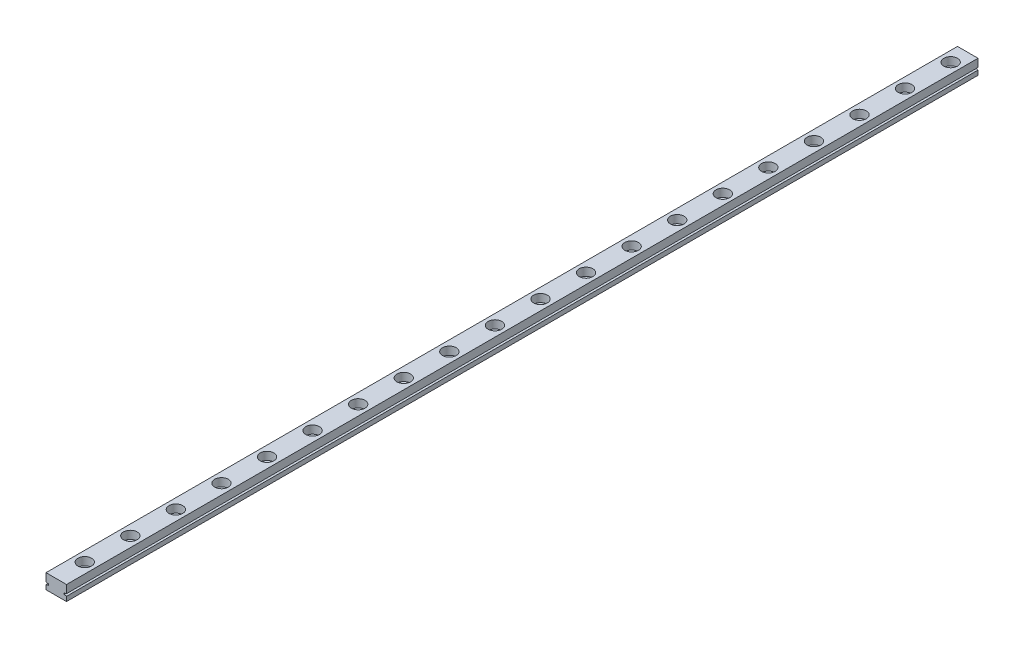
SolidWorks part; units mm, degrees
material "合金钢"
ref_plane "前视基准面" through (0, 0, 0) normal (0, 0, 1) x (1, 0, 0)
ref_plane "上视基准面" through (0, 0, 0) normal (0, 1, 0) x (1, 0, 0)
ref_plane "右视基准面" through (0, 0, 0) normal (1, 0, 0) x (0, 0, -1)
sketch "草图1" plane through (0, 0, 0) normal (0, 0, 1) x (1, 0, 0)
  line L1 (-4.5, 3.25) -> (4.5, 3.25)
  line L2 (-4.5, 3.25) -> (-4.5, -3.25)
  line L3 (-4.5, -3.25) -> (4.5, -3.25)
  line L4 (4.5, 3.25) -> (4.5, -3.25)
  line L5 (-4.5, 3.25) -> (4.5, -3.25) construction
  line L6 (-4.5, -3.25) -> (4.5, 3.25) construction
  point P0 (0, 0)
  dimension "D1" = 6.5
  dimension "D2" = 9
extrude "凸台-拉伸1" add sketch "草图1" along normal blind 400
sketch "草图2" plane through (0, 3.25, 0) normal (0, 1, 0) x (1, 0, 0)
  line L0 (0, 0) -> (0, -84.8716) construction
  line L1 (4.5, 0) -> (-4.5, 0) construction
  circle A0 centre (0, -7.5) radius 1.75
  circle A1 centre (0, -27.5) radius 1.75
  circle A2 centre (0, -47.5) radius 1.75
  circle A3 centre (0, -67.5) radius 1.75
  circle A4 centre (0, -87.5) radius 1.75
  circle A5 centre (0, -107.5) radius 1.75
  circle A6 centre (0, -127.5) radius 1.75
  circle A7 centre (0, -147.5) radius 1.75
  circle A8 centre (0, -167.5) radius 1.75
  circle A9 centre (0, -187.5) radius 1.75
  circle A10 centre (0, -207.5) radius 1.75
  circle A11 centre (0, -227.5) radius 1.75
  circle A12 centre (0, -247.5) radius 1.75
  circle A13 centre (0, -267.5) radius 1.75
  circle A14 centre (0, -287.5) radius 1.75
  circle A15 centre (0, -307.5) radius 1.75
  circle A16 centre (0, -327.5) radius 1.75
  circle A17 centre (0, -347.5) radius 1.75
  circle A18 centre (0, -367.5) radius 1.75
  dimension "D1" = 3.5
  dimension "D2" = 7.5
  dimension "D4" = 20
  dimension "D3" = 19
extrude "切除-拉伸1" cut sketch "草图2" against normal through all
sketch "草图3" plane through (0, 3.25, 0) normal (0, 1, 0) x (1, 0, 0)
  circle A0 centre (0, -7.5) radius 3
  circle A1 centre (0, -27.5) radius 3
  circle A2 centre (0, -47.5) radius 3
  circle A3 centre (0, -67.5) radius 3
  circle A4 centre (0, -87.5) radius 3
  circle A5 centre (0, -107.5) radius 3
  circle A6 centre (0, -127.5) radius 3
  circle A7 centre (0, -147.5) radius 3
  circle A8 centre (0, -167.5) radius 3
  circle A9 centre (0, -187.5) radius 3
  circle A10 centre (0, -207.5) radius 3
  circle A11 centre (0, -227.5) radius 3
  circle A12 centre (0, -247.5) radius 3
  circle A13 centre (0, -267.5) radius 3
  circle A14 centre (0, -287.5) radius 3
  circle A15 centre (0, -307.5) radius 3
  circle A16 centre (0, -327.5) radius 3
  circle A17 centre (0, -347.5) radius 3
  circle A18 centre (0, -367.5) radius 3
  circle A19 centre (0, -387.5) radius 3
  dimension "D1" = 6
  dimension "D3" = 20
  dimension "D2" = 20
extrude "切除-拉伸2" cut sketch "草图3" against normal blind 3.5
sketch "草图4" plane through (0, 0, 0) normal (0, 0, -1) x (-1, 0, 0)
  line L0 (0, 3.25) -> (0, -3.25) construction
  line L1 (-4.5, 3.25) -> (4.5, 3.25) construction
  line L2 (4.5, -3.25) -> (-4.5, -3.25) construction
  line L3 (4.5, -0.25) -> (3.5, -0.45)
  line L4 (4.5, 3.25) -> (4.5, -3.25) construction
  line L5 (3.5, -0.45) -> (3.5, -1.05)
  line L6 (3.5, -1.05) -> (4.5, -1.25)
  line L7 (3.5, -0.75) -> (7.9936, -0.75) construction
  line L8 (4.5, -0.25) -> (4.5, -1.25)
  line L9 (-4.5, -0.25) -> (-3.5, -0.45)
  line L10 (-3.5, -0.45) -> (-3.5, -1.05)
  line L11 (-3.5, -1.05) -> (-4.5, -1.25)
  line L12 (-4.5, -0.25) -> (-4.5, -1.25)
  dimension "D1" = 1
  dimension "D2" = 1
  dimension "D3" = 0.6
  dimension "D4" = 4
extrude "切除-拉伸3" cut sketch "草图4" against normal through all
sketch "草图5" plane through (0, -0.25, 0) normal (0, 1, 0) x (1, 0, 0)
  circle A0 centre (0, -387.5) radius 1.75
  circle A1 centre (0, -387.5) radius 3 construction
  dimension "D1" = 3.5
extrude "切除-拉伸4" cut sketch "草图5" against normal blind 10
